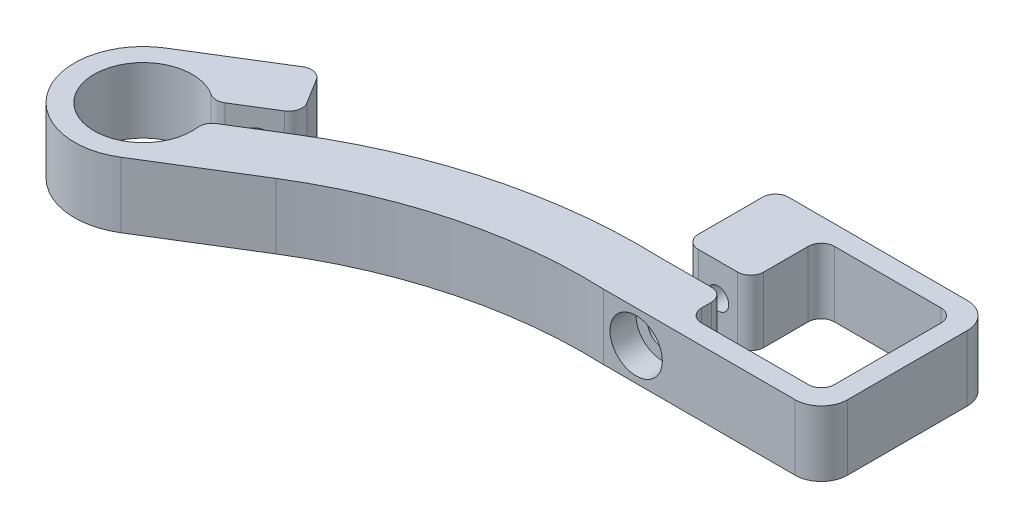
SolidWorks part; units mm, degrees
material "Сплав 2024"
ref_plane "Спереди" through (0, 0, 0) normal (0, 0, 1) x (1, 0, 0)
ref_plane "Сверху" through (0, 0, 0) normal (0, 1, 0) x (1, 0, 0)
ref_plane "Справа" through (0, 0, 0) normal (1, 0, 0) x (0, 0, -1)
sketch "Эскиз1" plane through (0, 0, 0) normal (0, 1, 0) x (1, 0, 0)
  line L0 (3, 3) -> (-23.3, 3)
  line L1 (0, 0) -> (-20.3, 0)
  line L2 (0, 0) -> (0, -20.3)
  line L3 (0, -20.3) -> (-20.3, -20.3)
  line L4 (-20.3, 0) -> (-20.3, -10.8)
  line L6 (3, -23.3) -> (-23.3, -23.3)
  line L7 (3, 3) -> (3, -23.3)
  line L8 (-20.3, 0) -> (0, -20.3) construction
  line L9 (0, 0) -> (-20.3, -20.3) construction
  line L10 (-112.7498, -23.3) -> (6.9459, -23.3) construction
  line L11 (-82.9486, -31.7049) -> (-74.4393, -26.452)
  line L12 (-84.6345, -42.7347) -> (-69.9744, -33.6849)
  line L13 (-85.0497, -28.3012) -> (-76.5404, -23.0483)
  line L14 (-95.6655, -24.8653) -> (-81.0054, -15.8155)
  line L15 (-76.5404, -23.0483) -> (-81.0054, -15.8155)
  line L16 (-83.0757, -12.4617) -> (-56.9698, -54.7516) construction
  line L17 (-23.3, -23.3) -> (-30.3, -23.3)
  line L18 (-30.3, -14.8) -> (-20.3, -14.8)
  line L19 (-30.3, 9.774) -> (-30.3, -38.2405) construction
  line L20 (-30.3, 3) -> (-23.3, 3)
  line L21 (-30.3, -10.8) -> (-20.3, -10.8)
  line L22 (-30.3, 3) -> (-30.3, -10.8)
  line L23 (-20.3, -14.8) -> (-20.3, -20.3)
  line L24 (-23.3, 3) -> (-23.3, -23.3) construction
  line L26 (-20.3, 0) -> (-20.3, -20.3) construction
  arc A0 (-85.0497, -28.3012) -> (-82.9486, -31.7049) centre (-90.15, -33.8) ccw
  arc A1 (-95.6655, -24.8653) -> (-84.6345, -42.7347) centre (-90.15, -33.8) ccw
  arc A2 (-69.9744, -33.6849) -> (-30.3, -23.3) centre (-33.1736, -93.3) cw
  arc A3 (-74.4393, -26.452) -> (-30.3, -14.8) centre (-33.1934, -93.2679) cw
  circle A5 centre (-90.15, -33.8) radius 10.5 construction
  circle A6 centre (-90.15, -33.8) radius 7.5 construction
  point P12 (-82.9777, -31.6072)
  point P13 (-82.4294, -26.6836)
  point P17 (-10.15, -10.15)
  point P20 (-82.9486, -31.7049)
  point P25 (-85.0497, -28.3012)
  point P27 (-80.3283, -30.0874)
  point P28 (-84.6345, -42.7347)
  point P29 (-95.6655, -24.8653)
  point P43 (-80.1088, -30.7301)
  dimension "D4" = 15
  dimension "D6" = 80
  dimension "D15" = 70
  dimension "D1" = 20.3
  dimension "D2" = 20.3
  dimension "D7" = 8.5
  dimension "D8" = 8.5
  dimension "D9" = 10
  dimension "D10" = 10
  dimension "D11" = 10
  dimension "D12" = 8.5
  dimension "D14" = 4
  dimension "D3" = 3
  dimension "D5" = 3
extrude "Бобышка-Вытянуть2" add sketch "Эскиз1" along normal blind 10
sketch "Эскиз3" plane through (0, 0, 23.3) normal (0, 0, 1) x (1, 0, 0)
  line L0 (3, 5) -> (-30.3, 5) construction
  line L1 (3, 10) -> (3, 0) construction
  line L2 (-30.3, 10) -> (-30.3, 0) construction
  line L3 (-25.3, 10) -> (-25.3, 0) construction
  line L4 (-30.3, 10) -> (3, 10) construction
  line L5 (-30.3, 0) -> (3, 0) construction
  dimension "D1" = 5
sketch "Эскиз2" plane through (-15.2821, 0, -24.756) normal (-0.5253, 0, -0.8509) x (-0.8509, 0, 0.5253)
  line L0 (77.2373, 5) -> (94.4657, 5) construction
  line L1 (77.2373, 10) -> (77.2373, 0) construction
  line L2 (94.4657, 10) -> (94.4657, 0) construction
  line L3 (82.2373, 10) -> (82.2373, 0) construction
  line L6 (77.2373, 10) -> (94.4657, 10) construction
  line L7 (77.2373, 0) -> (94.4657, 0) construction
  line L8 (77.2373, 10) -> (77.2373, 0) construction
  dimension "D1" = 5
hole_wizard "Отверстие обработанное метчиком M4x0.72" positions "Эскиз5" profile "Эскиз4" tap size "M4x0.7" standard "Ansi Metric"
sketch "Эскиз5" plane through (1.8042, -2.8232, 10.8) normal (0, 0, 1) x (1, 0, 0)
  line L0 (-27.1042, 12.8232) -> (-27.1042, 2.8232) construction
  line L1 (1.1958, 7.8232) -> (-32.1042, 7.8232) construction
  point P0 (-27.1042, 7.8232)
sketch "Эскиз4" plane through (-25.3, 5, 10.8) normal (1, 0, 0) x (0, -1, 0)
  line L0 (0, 0) -> (0, 9.5914)
  line L1 (0, 9.5914) -> (1.65, 8.6)
  line L2 (1.65, 8.6) -> (1.65, 0)
  line L5 (1.65, 0) -> (0, 0)
  line L10 (0, 9.5914) -> (-1.65, 8.6) construction
  line L11 (0, -6.35) -> (0, 107.95) construction
  dimension "Диаметр сверла" = 3.3
  dimension "Глубина сверла" = 8.6
  dimension "Угол заточки сверла" = 118
cosmetic thread "Отверстие резьбы2" parameters "D1"=8, "D2"=4
hole_wizard "Отверстие обработанное метчиком M4x0.71" positions "Эскиз7" profile "Эскиз6" tap size "M4x0.7" standard "Ansi Metric"
sketch "Эскиз7" plane through (-6.0319, 0.8585, -15.7763) normal (-0.5253, 0, -0.8509) x (-0.8509, 0, 0.5253)
  line L0 (80.3916, 4.1415) -> (97.62, 4.1415) construction
  line L1 (85.3916, 9.1415) -> (85.3916, -0.8585) construction
  point P0 (85.3916, 4.1415)
sketch "Эскиз6" plane through (-78.6939, 5, 29.0785) normal (0, 1, 0) x (-0.8509, 0, 0.5253)
  line L0 (0, 0) -> (0, 8.4914)
  line L1 (0, 8.4914) -> (1.65, 7.5)
  line L2 (1.65, 7.5) -> (1.65, 0)
  line L5 (1.65, 0) -> (0, 0)
  line L10 (0, 8.4914) -> (-1.65, 7.5) construction
  line L11 (0, -6.35) -> (0, 107.95) construction
  dimension "Диаметр сверла" = 3.3
  dimension "Глубина сверла" = 7.5
  dimension "Угол заточки сверла" = 118
cosmetic thread "Отверстие резьбы1" parameters "D1"=5, "D2"=4
hole_wizard "Цековка для винта с внутренним шестигранником M41" positions "Трехмерный эскиз1" profile "Эскиз8" counterbore size "M4" standard "Ansi Metric"
sketch3d "Трехмерный эскиз1"
  line L0 (-25.3, 10, 23.3) -> (-25.3, 0, 23.3) construction
  line L1 (3, 5, 23.3) -> (-30.3, 5, 23.3) construction
  point P0 (-25.3, 5, 23.3)
sketch "Эскиз8" plane through (-25.3, 5, 23.3) normal (1, 0, 0) x (0, -1, 0)
  line L0 (0, 0) -> (0, 8.5)
  line L1 (0, 8.5) -> (2.25, 8.5)
  line L3 (2.25, 8.5) -> (2.25, 4)
  line L4 (2.25, 4) -> (4, 4)
  line L5 (4, 4) -> (4, 0)
  line L7 (4, 0) -> (0, 0)
  line L11 (0, -6.35) -> (0, 107.95) construction
  dimension "Диаметр сквозного отверстия" = 4.5
  dimension "Глубина сквозного отверстия" = 8.5
  dimension "Диаметр цековки" = 8
  dimension "Глубина цековки" = 4
hole_wizard "Отверстие с зазором M41" positions "Эскиз10" profile "Эскиз9" hole size "M4" standard "Ansi Metric"
sketch "Эскиз10" plane through (-15.2821, 0, -24.756) normal (-0.5253, 0, -0.8509) x (-0.8509, 0, 0.5253)
  line L0 (77.2373, 5) -> (94.4657, 5) construction
  line L1 (82.2373, 10) -> (82.2373, 0) construction
  point P0 (82.2373, 5)
sketch "Эскиз9" plane through (-85.26, 5, 18.4419) normal (0, 1, 0) x (-0.8509, 0, 0.5253)
  line L0 (0, 0) -> (0, 9.8509)
  line L1 (0, 9.8509) -> (2.25, 8.499)
  line L2 (2.25, 8.499) -> (2.25, 0)
  line L5 (2.25, 0) -> (0, 0)
  line L10 (0, 9.8509) -> (-2.25, 8.499) construction
  line L11 (0, -6.35) -> (0, 107.95) construction
  dimension "Диаметр отверстия" = 4.5
  dimension "Глубина отверстия" = 8.499
  dimension "Угол заточки сверла" = 118
fillet "Скругление4" radius 4 2 edges at (3, 5, 23.3) (3, 5, -3)
fillet "Скругление3" radius 2 12 edges at (-81.0054, 5, 15.8155) (-76.5404, 5, 23.0483) (-82.9486, 5, 31.7049) (-85.0497, 5, 28.3012) (-20.3, 5, 10.8) (-20.3, 5, 14.8) (0, 5, 20.3) (-20.3, 5, 20.3) (-20.3, 5, 0) (0, 5, 0) (-30.3, 5, 10.8) (-30.3, 5, -3)
sketch "Эскиз11" plane through (0, 0, 0) normal (0, 1, 0) x (1, 0, 0)
  line L0 (3, -19.3) -> (3, -1) construction
  line L1 (-1, 3) -> (-28.3, 3) construction
  point P0 (3, 3)
